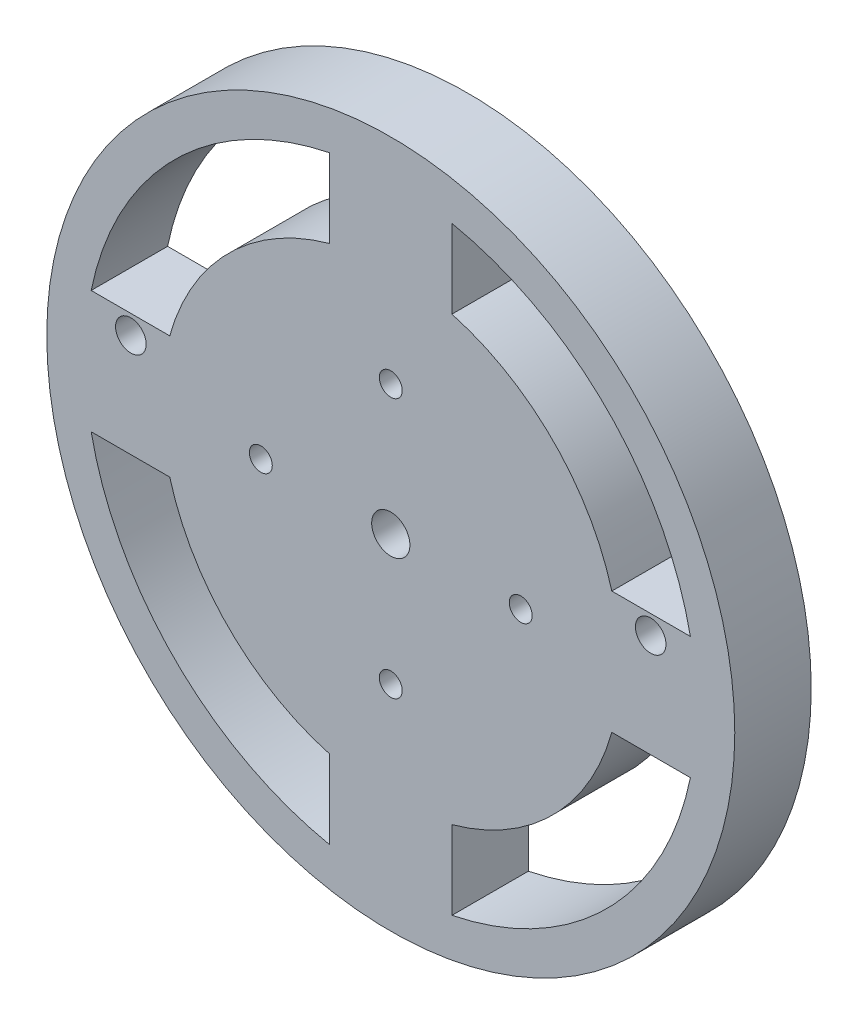
SolidWorks part; units mm, degrees
ref_plane "Front Plane" through (0, 0, 0) normal (0, 0, 1) x (1, 0, 0)
ref_plane "Top Plane" through (0, 0, 0) normal (0, 1, 0) x (1, 0, 0)
ref_plane "Right Plane" through (0, 0, 0) normal (1, 0, 0) x (0, 0, -1)
sketch "Sketch1" plane through (0, 0, 0) normal (0, 0, 1) x (1, 0, 0)
  line L0 (0, 57.5241) -> (0, -57.5241) construction
  line L1 (-61.4517, 0) -> (61.4517, 0) construction
  line L2 (28.9137, 8) -> (39.1918, 8)
  line L3 (28.9137, -8) -> (39.1918, -8)
  line L4 (8, -28.9137) -> (8, -39.1918)
  line L5 (-8, -28.9137) -> (-8, -39.1918)
  line L6 (-39.1918, 8) -> (-28.9137, 8)
  line L7 (-39.1918, -8) -> (-28.9137, -8)
  line L19 (8, 39.1918) -> (8, 28.9137)
  line L20 (-8, 39.1918) -> (-8, 28.9137)
  circle A0 centre (0, 0) radius 45
  circle A1 centre (0, 0) radius 2.5
  circle A2 centre (0, 17) radius 1.5
  circle A3 centre (17, 0) radius 1.5
  circle A4 centre (0, -17) radius 1.5
  circle A5 centre (-17, 0) radius 1.5
  arc A6 (-28.9137, -8) -> (-8, -28.9137) centre (0, 0) ccw
  arc A7 (-39.1918, -8) -> (-8, -39.1918) centre (0, 0) ccw
  arc A8 (-8, 39.1918) -> (-39.1918, 8) centre (0, 0) ccw
  arc A9 (-8, 28.9137) -> (-28.9137, 8) centre (0, 0) ccw
  arc A10 (39.1918, 8) -> (8, 39.1918) centre (0, 0) ccw
  arc A11 (28.9137, 8) -> (8, 28.9137) centre (0, 0) ccw
  arc A12 (8, -39.1918) -> (39.1918, -8) centre (0, 0) ccw
  arc A13 (8, -28.9137) -> (28.9137, -8) centre (0, 0) ccw
  point P15 (-4.7966, 0.2687)
  point P16 (-8, 57.5241)
  point P18 (-8, -57.5241)
  point P19 (-61.4517, -8)
  point P20 (61.4517, -8)
  point P21 (8, 57.5241)
  point P22 (-34.0528, -8)
  point P23 (8, -57.5241)
  point P24 (-61.4517, 8)
  point P25 (61.4517, 8)
  dimension "D1" = 90
  dimension "D2" = 3
  dimension "D3" = 5
  dimension "D8" = 60
  dimension "D11" = 80
  dimension "D12" = 8
  dimension "D4" = 17
  dimension "D5" = 17
  dimension "D6" = 17
  dimension "D7" = 17
  dimension "D9" = 8
  dimension "D10" = 8
  dimension "D13" = 8
  dimension "D14" = 8
  dimension "D15" = 8
  dimension "D16" = 8
extrude "Boss-Extrude1" add sketch "Sketch1" along normal blind 10
sketch "Sketch3" plane through (0, 0, 10) normal (0, 0, 1) x (1, 0, 0)
  line L0 (0, 34.0183) -> (0, -25.2417) construction
  line L2 (-39.1918, 8) -> (-28.9137, 8) construction
  circle A0 centre (-34, 5.5) radius 2
  circle A1 centre (34, 5.5) radius 2
  dimension "D1" = 4
  dimension "D2" = 4
  dimension "D5" = 0.5
  dimension "D3" = 34
  dimension "D4" = 34
extrude "Cut-Extrude1" cut sketch "Sketch3" against normal blind 10
